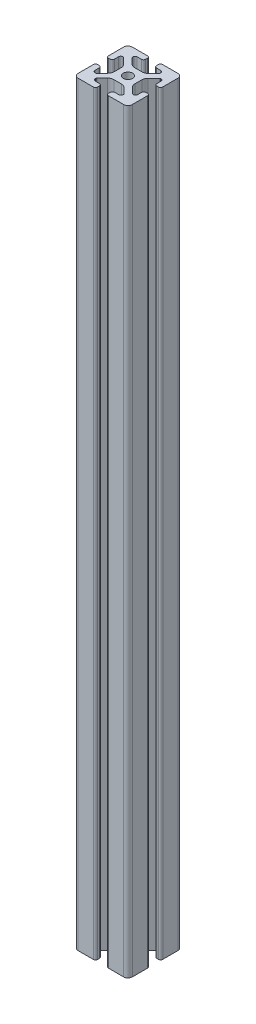
SolidWorks part; units mm, degrees
ref_plane "Front Plane" through (0, 0, 0) normal (0, 0, 1) x (1, 0, 0)
ref_plane "Top Plane" through (0, 0, 0) normal (0, 1, 0) x (1, 0, 0)
ref_plane "Right Plane" through (0, 0, 0) normal (1, 0, 0) x (0, 0, -1)
sketch "Sketch1" plane through (0, 0, 0) normal (0, 0, 1) x (1, 0, 0)
  line L0 (0, 0) -> (0, 558.8)
  dimension "D1" = 558.8
other "40 series 4040(1)"
ref_plane "Plane1" through (0, 0, 0) normal (0, 1, 0) x (-1, 0, 0)
sketch "Sketch11" plane through (0, 0, 0) normal (0, 1, 0) x (-1, 0, 0)
  line L88 (-5.63, -15.5246) -> (-8.715, -15.5246)
  line L89 (-10.285, -13.9546) -> (-10.285, -13.4925)
  line L90 (-10.0624, -12.9551) -> (-6.2171, -9.1098)
  line L91 (-2.7773, -7.685) -> (2.7773, -7.685)
  line L92 (6.2171, -9.1098) -> (10.0624, -12.9551)
  line L93 (10.285, -13.4925) -> (10.285, -13.9546)
  line L94 (8.715, -15.5246) -> (5.63, -15.5246)
  line L95 (4.06, -17.0946) -> (4.06, -18.43)
  line L96 (5.63, -20) -> (16.83, -20)
  line L97 (20, -16.83) -> (20, -5.63)
  line L98 (18.43, -4.06) -> (17.25, -4.06)
  line L99 (15.68, -5.63) -> (15.68, -8.7154)
  line L100 (14.11, -10.2854) -> (13.6201, -10.2854)
  line L101 (13.1637, -9.947) -> (9.0762, -5.8595)
  line L102 (7.685, -2.5008) -> (7.685, 2.5008)
  line L103 (9.0762, 5.8595) -> (13.2795, 10.0628)
  line L104 (13.8169, 10.2854) -> (14.11, 10.2854)
  line L105 (15.68, 8.7154) -> (15.68, 5.63)
  line L106 (17.25, 4.06) -> (18.43, 4.06)
  line L107 (20, 5.63) -> (20, 16.83)
  line L108 (16.83, 20) -> (5.63, 20)
  line L109 (4.06, 18.43) -> (4.06, 17.0946)
  line L110 (5.63, 15.5246) -> (8.715, 15.5246)
  line L111 (10.285, 13.9546) -> (10.285, 13.4925)
  line L112 (10.0624, 12.9551) -> (6.2171, 9.1098)
  line L113 (2.7773, 7.685) -> (-2.7773, 7.685)
  line L114 (-6.2171, 9.1098) -> (-10.0624, 12.9551)
  line L115 (-10.285, 13.4925) -> (-10.285, 13.9546)
  line L116 (-8.715, 15.5246) -> (-5.63, 15.5246)
  line L117 (-4.06, 17.0946) -> (-4.06, 18.43)
  line L118 (-5.63, 20) -> (-16.83, 20)
  line L119 (-20, 16.83) -> (-20, 5.573)
  line L120 (-18.43, 4.003) -> (-17.25, 4.003)
  line L121 (-15.68, 5.573) -> (-15.68, 8.4757)
  line L122 (-14.0552, 10.0447) -> (-13.7199, 10.033)
  line L123 (-13.0405, 9.8238) -> (-9.0762, 5.8595)
  line L124 (-7.685, 2.5008) -> (-7.685, -2.5008)
  line L125 (-9.0762, -5.8595) -> (-13.2795, -10.0628)
  line L126 (-13.8169, -10.2854) -> (-14.11, -10.2854)
  line L127 (-15.68, -8.7154) -> (-15.68, -5.7579)
  line L128 (-17.25, -4.1204) -> (-18.43, -4.1204)
  line L129 (-20, -5.7579) -> (-20, -17.0184)
  line L130 (-16.6746, -20) -> (-5.63, -20)
  line L131 (-4.06, -18.43) -> (-4.06, -17.0946)
  circle A1 centre (0, 0) radius 3.4
  arc A88 (-4.06, -17.0946) -> (-5.63, -15.5246) centre (-5.63, -17.0946) ccw
  arc A89 (-10.285, -13.9546) -> (-8.715, -15.5246) centre (-8.715, -13.9546) ccw
  arc A90 (-10.0624, -12.9551) -> (-10.285, -13.4925) centre (-9.525, -13.4925) ccw
  arc A91 (-2.7773, -7.685) -> (-6.2171, -9.1098) centre (-2.7773, -12.5496) ccw
  arc A92 (6.2171, -9.1098) -> (2.7773, -7.685) centre (2.7773, -12.5496) ccw
  arc A93 (10.285, -13.4925) -> (10.0624, -12.9551) centre (9.525, -13.4925) ccw
  arc A94 (8.715, -15.5246) -> (10.285, -13.9546) centre (8.715, -13.9546) ccw
  arc A95 (5.63, -15.5246) -> (4.06, -17.0946) centre (5.63, -17.0946) ccw
  arc A96 (4.06, -18.43) -> (5.63, -20) centre (5.63, -18.43) ccw
  arc A97 (16.83, -20) -> (20, -16.83) centre (16.83, -16.83) ccw
  arc A98 (20, -5.63) -> (18.43, -4.06) centre (18.43, -5.63) ccw
  arc A99 (17.25, -4.06) -> (15.68, -5.63) centre (17.25, -5.63) ccw
  arc A100 (14.11, -10.2854) -> (15.68, -8.7154) centre (14.11, -8.7154) ccw
  arc A101 (13.1637, -9.947) -> (13.6201, -10.2854) centre (13.8117, -9.55) ccw
  arc A102 (7.685, -2.5008) -> (9.0762, -5.8595) centre (12.435, -2.5008) ccw
  arc A103 (9.0762, 5.8595) -> (7.685, 2.5008) centre (12.435, 2.5008) ccw
  arc A104 (13.8169, 10.2854) -> (13.2795, 10.0628) centre (13.8169, 9.5254) ccw
  arc A105 (15.68, 8.7154) -> (14.11, 10.2854) centre (14.11, 8.7154) ccw
  arc A106 (15.68, 5.63) -> (17.25, 4.06) centre (17.25, 5.63) ccw
  arc A107 (18.43, 4.06) -> (20, 5.63) centre (18.43, 5.63) ccw
  arc A108 (20, 16.83) -> (16.83, 20) centre (16.83, 16.83) ccw
  arc A109 (5.63, 20) -> (4.06, 18.43) centre (5.63, 18.43) ccw
  arc A110 (4.06, 17.0946) -> (5.63, 15.5246) centre (5.63, 17.0946) ccw
  arc A111 (10.285, 13.9546) -> (8.715, 15.5246) centre (8.715, 13.9546) ccw
  arc A112 (10.0624, 12.9551) -> (10.285, 13.4925) centre (9.525, 13.4925) ccw
  arc A113 (2.7773, 7.685) -> (6.2171, 9.1098) centre (2.7773, 12.5496) ccw
  arc A114 (-6.2171, 9.1098) -> (-2.7773, 7.685) centre (-2.7773, 12.5496) ccw
  arc A115 (-10.285, 13.4925) -> (-10.0624, 12.9551) centre (-9.525, 13.4925) ccw
  arc A116 (-8.715, 15.5246) -> (-10.285, 13.9546) centre (-8.715, 13.9546) ccw
  arc A117 (-5.63, 15.5246) -> (-4.06, 17.0946) centre (-5.63, 17.0946) ccw
  arc A118 (-4.06, 18.43) -> (-5.63, 20) centre (-5.63, 18.43) ccw
  arc A119 (-16.83, 20) -> (-20, 16.83) centre (-16.83, 16.83) ccw
  arc A120 (-20, 5.573) -> (-18.43, 4.003) centre (-18.43, 5.573) ccw
  arc A121 (-17.25, 4.003) -> (-15.68, 5.573) centre (-17.25, 5.573) ccw
  arc A122 (-14.0552, 10.0447) -> (-15.68, 8.4757) centre (-14.11, 8.4757) ccw
  arc A123 (-13.0405, 9.8238) -> (-13.7199, 10.033) centre (-13.5779, 9.2864) ccw
  arc A124 (-7.685, 2.5008) -> (-9.0762, 5.8595) centre (-12.435, 2.5008) ccw
  arc A125 (-9.0762, -5.8595) -> (-7.685, -2.5008) centre (-12.435, -2.5008) ccw
  arc A126 (-13.8169, -10.2854) -> (-13.2795, -10.0628) centre (-13.8169, -9.5254) ccw
  arc A127 (-15.68, -8.7154) -> (-14.11, -10.2854) centre (-14.11, -8.7154) ccw
  arc A128 (-15.68, -5.7579) -> (-17.25, -4.1204) centre (-17.2485, -5.6904) ccw
  arc A129 (-18.43, -4.1204) -> (-20, -5.7579) centre (-18.4315, -5.6904) ccw
  arc A130 (-20, -17.0184) -> (-16.6746, -20) centre (-16.8354, -16.8341) ccw
  arc A131 (-5.63, -20) -> (-4.06, -18.43) centre (-5.63, -18.43) ccw
  point P5 (0, 20)
  point P15 (-20, 20)
  point P20 (20, 20)
  point P25 (20, 0)
  point P30 (20, -20)
  point P35 (0, -20)
  point P40 (-20, -20)
  point P45 (-20, 0)
  point P50 (0, 0)
  point P55 (0, 0)
